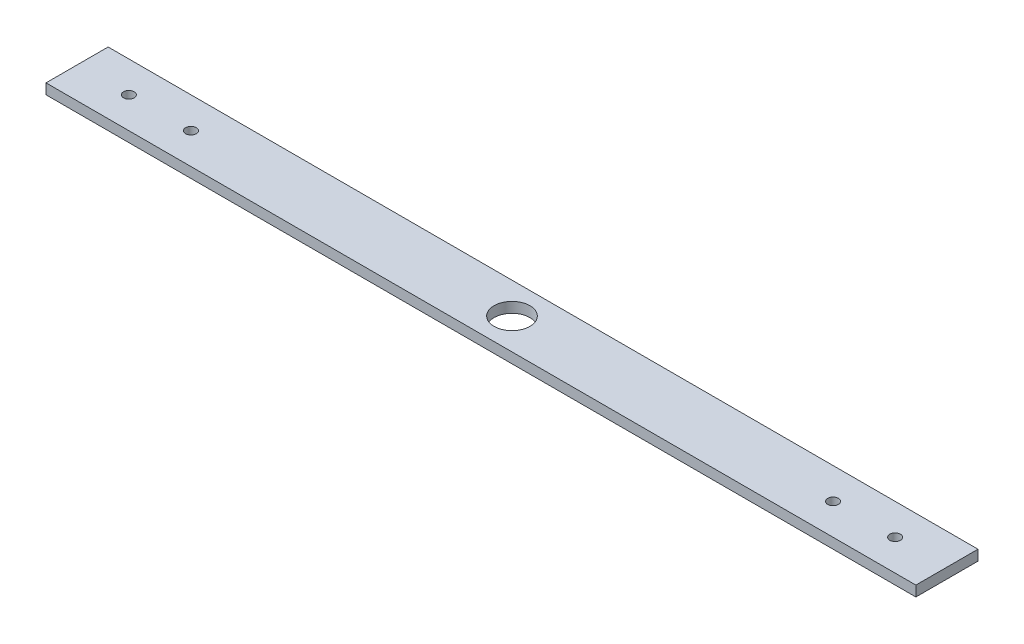
SolidWorks part; units mm, degrees
material "6061-T6 (SS)"
ref_plane "Front Plane" through (0, 0, 0) normal (0, 0, 1) x (1, 0, 0)
ref_plane "Top Plane" through (0, 0, 0) normal (0, 1, 0) x (1, 0, 0)
ref_plane "Right Plane" through (0, 0, 0) normal (1, 0, 0) x (0, 0, -1)
sketch "Sketch1" plane through (0, 0, 0) normal (0, 1, 0) x (1, 0, 0)
  line L1 (-266.7, 19.05) -> (266.7, 19.05)
  line L2 (-266.7, 19.05) -> (-266.7, -19.05)
  line L3 (-266.7, -19.05) -> (266.7, -19.05)
  line L4 (266.7, 19.05) -> (266.7, -19.05)
  line L5 (-266.7, 19.05) -> (266.7, -19.05) construction
  line L6 (-266.7, -19.05) -> (266.7, 19.05) construction
  point P0 (0, 0)
  dimension "D1" = 533.4
  dimension "D2" = 38.1
extrude "Boss-Extrude1" add sketch "Sketch1" along normal blind 6.35
sketch "Sketch2" plane through (0, 6.35, 0) normal (0, 1, 0) x (1, 0, 0)
  circle A0 centre (0, 0) radius 11
  dimension "D1" = 22
extrude "Cut-Extrude1" cut sketch "Sketch2" against normal blind 7.62
hole_wizard "F (0.257) Diameter Hole1" positions "Sketch4" profile "Sketch5" hole size "F" standard "ANSI Inch" end condition through all
sketch "Sketch4" plane through (0, 6.35, 0) normal (0, 1, 0) x (1, 0, 0)
  line L0 (266.7, -19.05) -> (266.7, 19.05) construction
  point P0 (234.95, 0)
  point P2 (196.85, 0)
  dimension "D1" = 31.75
  dimension "D2" = 69.85
sketch "Sketch5" plane through (234.95, 6.35, 0) normal (1, 0, 0) x (0, 0, 1)
  line L0 (0, 0) -> (0, 6.35)
  line L1 (0, 6.35) -> (3.2639, 6.35)
  line L2 (3.2639, 6.35) -> (3.2639, 0)
  line L5 (3.2639, 0) -> (0, 0)
  line L11 (0, -6.35) -> (0, 107.95) construction
  dimension "Thru Hole Dia." = 6.5278
  dimension "Thru Hole Depth" = 6.35
mirror "Mirror1" about plane through (0, 0, 0) normal (1, 0, 0) of "F (0.257) Diameter Hole1"
